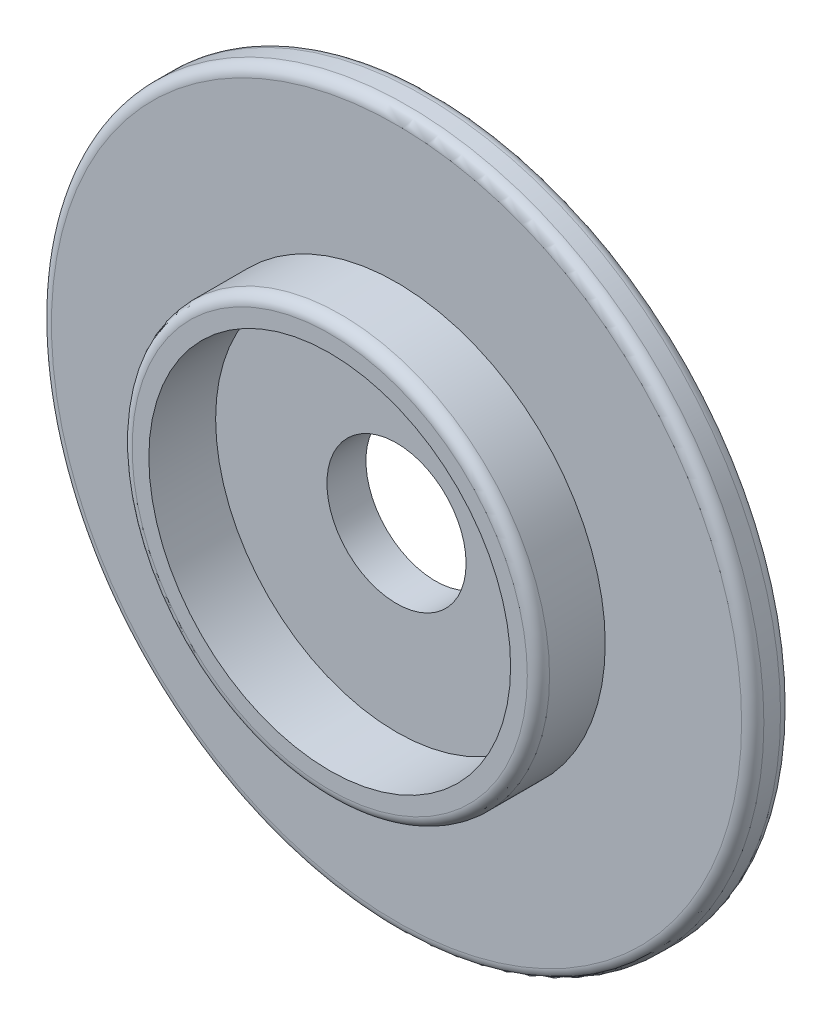
SolidWorks part; units mm, degrees
ref_plane "Front" through (0, 0, 0) normal (0, 0, 1) x (1, 0, 0)
ref_plane "Top" through (0, 0, 0) normal (0, 1, 0) x (1, 0, 0)
ref_plane "Right" through (0, 0, 0) normal (1, 0, 0) x (0, 0, -1)
sketch "Sketch1" plane through (0, 0, 0) normal (0, 0, 1) x (1, 0, 0)
  circle A0 centre (0, 0) radius 64
  dimension "D1" = 128
extrude "Boss-Extrude2" add sketch "Sketch1" along normal blind 7
sketch "Sketch3" plane through (0, 0, 7) normal (0, 0, 1) x (1, 0, 0)
  circle A0 centre (0, 0) radius 37.5
  circle A1 centre (0, 0) radius 32.5
  point P1 (0, 0)
  dimension "D1" = 75
  dimension "D2" = 5
extrude "Boss-Extrude3" add sketch "Sketch3" along normal blind 12
sketch "Sketch6" plane through (0, 0, 7) normal (0, 0, 1) x (1, 0, 0)
  circle A0 centre (0, 0) radius 12.5
  point P1 (0, 0)
  dimension "D1" = 25
extrude "Cut-Extrude1" cut sketch "Sketch6" against normal through all
fillet "Fillet1" radius 2 3 edges at (64, 0, 0) (64, 0, 7) (37.5, 0, 19)
